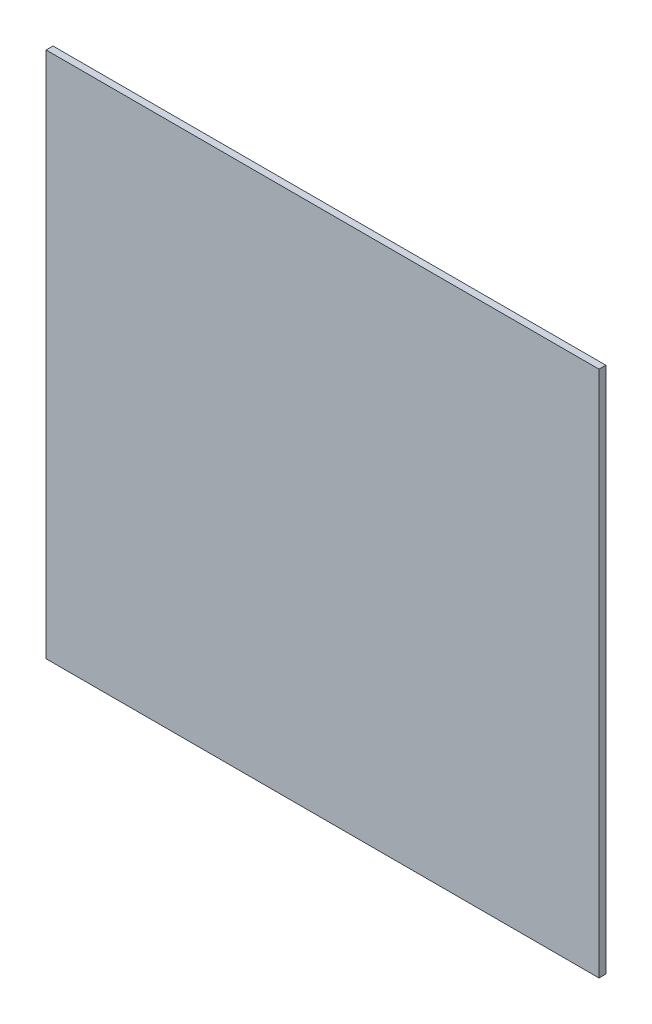
SolidWorks part; units mm, degrees
ref_plane "Front Plane" through (0, 0, 0) normal (0, 0, 1) x (1, 0, 0)
ref_plane "Top Plane" through (0, 0, 0) normal (0, 1, 0) x (1, 0, 0)
ref_plane "Right Plane" through (0, 0, 0) normal (1, 0, 0) x (0, 0, -1)
sketch "Sketch1" plane through (0, 0, 0) normal (0, 0, 1) x (1, 0, 0)
  line L1 (-479.425, -457.2) -> (479.425, -457.2)
  line L2 (-479.425, -457.2) -> (-479.425, 457.2)
  line L3 (-479.425, 457.2) -> (479.425, 457.2)
  line L4 (479.425, -457.2) -> (479.425, 457.2)
  line L5 (-479.425, -457.2) -> (479.425, 457.2) construction
  line L6 (-479.425, 457.2) -> (479.425, -457.2) construction
  point P0 (0, 0)
  dimension "D1" = 914.4
  dimension "D2" = 958.85
extrude "Boss-Extrude1" add sketch "Sketch1" along normal blind 11.9062
